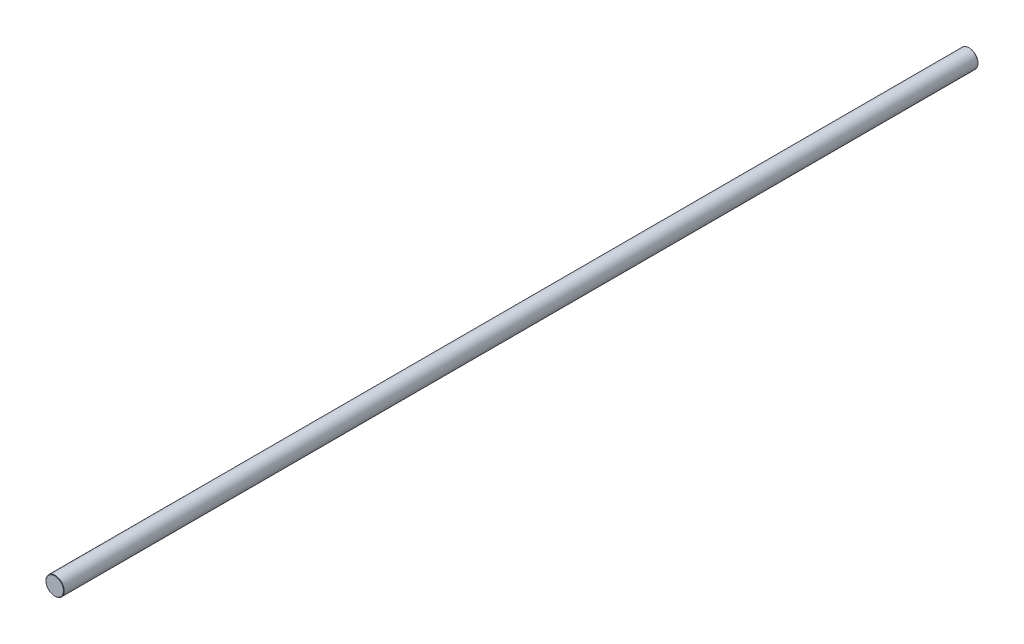
SolidWorks part; units mm, degrees
material "AISI 304"
ref_plane "Front Plane" through (0, 0, 0) normal (0, 0, 1) x (1, 0, 0)
ref_plane "Top Plane" through (0, 0, 0) normal (0, 1, 0) x (1, 0, 0)
ref_plane "Right Plane" through (0, 0, 0) normal (1, 0, 0) x (0, 0, -1)
sketch "Sketch1" plane through (0, 0, 0) normal (0, 0, 1) x (1, 0, 0)
  circle A1 centre (0, 0) radius 12.7
  dimension "D1" = 25.4
extrude "Boss-Extrude1" add sketch "Sketch1" along normal mid plane 1276
chamfer "Chamfer1" distance 0.5 angle 45 2 edges at (12.7, 0, -638) (12.7, 0, 638)
